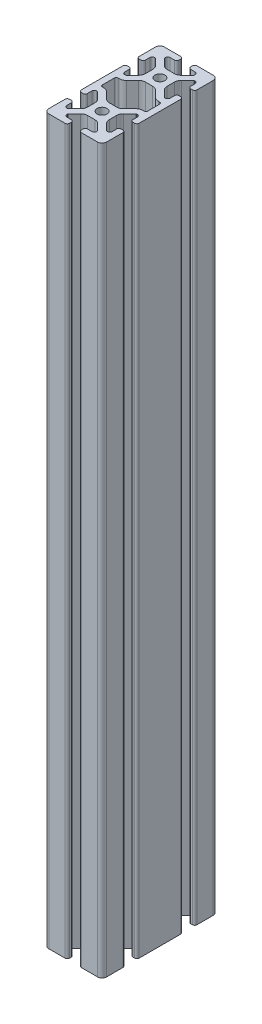
SolidWorks part; units mm, degrees
ref_plane "Front Plane" through (0, 0, 0) normal (0, 0, 1) x (1, 0, 0)
ref_plane "Top Plane" through (0, 0, 0) normal (0, 1, 0) x (1, 0, 0)
ref_plane "Right Plane" through (0, 0, 0) normal (1, 0, 0) x (0, 0, -1)
sketch3d "3DSketch1"
  line L0 (0, 0, 0) -> (0, 500, 0)
  dimension "D1" = 500
other "30 30-3060 PROFILE(1)"
ref_plane "Plane3" through (0, 0, 0) normal (0, 1, 0) x (1, 0, 0)
sketch "Sketch1" plane through (0, 0, 0) normal (0, 1, 0) x (1, 0, 0)
  line L0 (15.68, 24.125) -> (15.68, 15.875)
  line L1 (14.41, 14.605) -> (13.6545, 14.605)
  line L2 (10.0624, 13.1171) -> (5.8651, 8.9198)
  line L3 (2.5064, 7.5286) -> (-2.5064, 7.5286)
  line L4 (-5.8651, 8.9198) -> (-10.0624, 13.1171)
  line L5 (-13.6545, 14.605) -> (-14.41, 14.605)
  line L6 (-15.68, 15.875) -> (-15.68, 24.125)
  line L7 (-14.41, 25.395) -> (-13.6545, 25.395)
  line L8 (-10.0624, 26.8829) -> (-5.8651, 31.0802)
  line L9 (-2.5064, 32.4714) -> (2.5064, 32.4714)
  line L10 (5.8651, 31.0802) -> (10.0624, 26.8829)
  line L11 (13.6545, 25.395) -> (14.41, 25.395)
  line L12 (20, 5.63) -> (20, 34.37)
  line L13 (18.43, 35.94) -> (17.252, 35.94)
  line L14 (15.682, 34.37) -> (15.682, 31.285)
  line L15 (14.112, 29.715) -> (13.6545, 29.715)
  line L16 (13.1171, 29.9376) -> (8.9198, 34.1349)
  line L17 (7.5286, 37.4936) -> (7.5286, 42.5064)
  line L18 (8.9198, 45.8651) -> (13.1171, 50.0624)
  line L19 (13.6545, 50.285) -> (14.112, 50.285)
  line L20 (15.682, 48.715) -> (15.682, 45.63)
  line L21 (17.252, 44.06) -> (18.43, 44.06)
  line L22 (20, 45.63) -> (20, 56.83)
  line L23 (16.83, 60) -> (5.63, 60)
  line L24 (4.06, 58.43) -> (4.06, 57.252)
  line L25 (5.63, 55.682) -> (8.715, 55.682)
  line L26 (10.285, 54.112) -> (10.285, 53.6545)
  line L27 (10.0624, 53.1171) -> (5.8651, 48.9198)
  line L28 (2.5064, 47.5286) -> (-2.5064, 47.5286)
  line L29 (-5.8651, 48.9198) -> (-10.0624, 53.1171)
  line L30 (-10.285, 53.6545) -> (-10.285, 54.112)
  line L31 (-8.715, 55.682) -> (-5.63, 55.682)
  line L32 (-4.06, 57.252) -> (-4.06, 58.43)
  line L33 (-5.63, 60) -> (-16.83, 60)
  line L34 (-20, 56.83) -> (-20, 45.63)
  line L35 (-18.43, 44.06) -> (-17.252, 44.06)
  line L36 (-15.682, 45.63) -> (-15.682, 48.715)
  line L37 (-14.112, 50.285) -> (-13.6545, 50.285)
  line L38 (-13.1171, 50.0624) -> (-8.9198, 45.8651)
  line L39 (-7.5286, 42.5064) -> (-7.5286, 37.4936)
  line L40 (-8.9198, 34.1349) -> (-13.1171, 29.9376)
  line L41 (-13.6545, 29.715) -> (-14.112, 29.715)
  line L42 (-15.682, 31.285) -> (-15.682, 34.37)
  line L43 (-17.252, 35.94) -> (-18.43, 35.94)
  line L44 (-20, 34.37) -> (-20, 5.63)
  line L45 (-18.43, 4.06) -> (-17.252, 4.06)
  line L46 (-15.682, 5.63) -> (-15.682, 8.715)
  line L47 (-14.112, 10.285) -> (-13.6545, 10.285)
  line L48 (-13.1171, 10.0624) -> (-8.9198, 5.8651)
  line L49 (-7.5286, 2.5064) -> (-7.5286, -2.5064)
  line L50 (-8.9198, -5.8651) -> (-13.1171, -10.0624)
  line L51 (-13.6545, -10.285) -> (-14.112, -10.285)
  line L52 (-15.682, -8.715) -> (-15.682, -5.63)
  line L53 (-17.252, -4.06) -> (-18.43, -4.06)
  line L54 (-20, -5.63) -> (-20, -16.83)
  line L55 (-16.83, -20) -> (-5.63, -20)
  line L56 (-4.06, -18.43) -> (-4.06, -17.252)
  line L57 (-5.63, -15.682) -> (-8.715, -15.682)
  line L58 (-10.285, -14.112) -> (-10.285, -13.6545)
  line L59 (-10.0624, -13.1171) -> (-5.8651, -8.9198)
  line L60 (-2.5064, -7.5286) -> (2.5064, -7.5286)
  line L61 (5.8651, -8.9198) -> (10.0624, -13.1171)
  line L62 (10.285, -13.6545) -> (10.285, -14.112)
  line L63 (8.715, -15.682) -> (5.63, -15.682)
  line L64 (4.06, -17.252) -> (4.06, -18.43)
  line L65 (5.63, -20) -> (16.83, -20)
  line L66 (20, -16.83) -> (20, -5.63)
  line L67 (18.43, -4.06) -> (17.252, -4.06)
  line L68 (15.682, -5.63) -> (15.682, -8.715)
  line L69 (14.112, -10.285) -> (13.6545, -10.285)
  line L70 (13.1171, -10.0624) -> (8.9198, -5.8651)
  line L71 (7.5286, -2.5064) -> (7.5286, 2.5064)
  line L72 (8.9198, 5.8651) -> (13.1171, 10.0624)
  line L73 (13.6545, 10.285) -> (14.112, 10.285)
  line L74 (15.682, 8.715) -> (15.682, 5.63)
  line L75 (17.252, 4.06) -> (18.43, 4.06)
  circle A0 centre (0, 0) radius 3.4
  arc A1 (15.68, 24.125) -> (14.41, 25.395) centre (14.41, 24.125) ccw
  arc A2 (14.41, 14.605) -> (15.68, 15.875) centre (14.41, 15.875) ccw
  arc A3 (13.6545, 14.605) -> (10.0624, 13.1171) centre (13.6545, 9.525) ccw
  arc A4 (2.5064, 7.5286) -> (5.8651, 8.9198) centre (2.5064, 12.2786) ccw
  arc A5 (-5.8651, 8.9198) -> (-2.5064, 7.5286) centre (-2.5064, 12.2786) ccw
  arc A6 (-10.0624, 13.1171) -> (-13.6545, 14.605) centre (-13.6545, 9.525) ccw
  arc A7 (-15.68, 15.875) -> (-14.41, 14.605) centre (-14.41, 15.875) ccw
  arc A8 (-14.41, 25.395) -> (-15.68, 24.125) centre (-14.41, 24.125) ccw
  arc A9 (-13.6545, 25.395) -> (-10.0624, 26.8829) centre (-13.6545, 30.475) ccw
  arc A10 (-2.5064, 32.4714) -> (-5.8651, 31.0802) centre (-2.5064, 27.7214) ccw
  arc A11 (5.8651, 31.0802) -> (2.5064, 32.4714) centre (2.5064, 27.7214) ccw
  arc A12 (10.0624, 26.8829) -> (13.6545, 25.395) centre (13.6545, 30.475) ccw
  circle A13 centre (0, 40) radius 3.4
  arc A14 (18.43, 4.06) -> (20, 5.63) centre (18.43, 5.63) ccw
  arc A15 (20, 34.37) -> (18.43, 35.94) centre (18.43, 34.37) ccw
  arc A16 (17.252, 35.94) -> (15.682, 34.37) centre (17.252, 34.37) ccw
  arc A17 (14.112, 29.715) -> (15.682, 31.285) centre (14.112, 31.285) ccw
  arc A18 (13.1171, 29.9376) -> (13.6545, 29.715) centre (13.6545, 30.475) ccw
  arc A19 (7.5286, 37.4936) -> (8.9198, 34.1349) centre (12.2786, 37.4936) ccw
  arc A20 (8.9198, 45.8651) -> (7.5286, 42.5064) centre (12.2786, 42.5064) ccw
  arc A21 (13.6545, 50.285) -> (13.1171, 50.0624) centre (13.6545, 49.525) ccw
  arc A22 (15.682, 48.715) -> (14.112, 50.285) centre (14.112, 48.715) ccw
  arc A23 (15.682, 45.63) -> (17.252, 44.06) centre (17.252, 45.63) ccw
  arc A24 (18.43, 44.06) -> (20, 45.63) centre (18.43, 45.63) ccw
  arc A25 (20, 56.83) -> (16.83, 60) centre (16.83, 56.83) ccw
  arc A26 (5.63, 60) -> (4.06, 58.43) centre (5.63, 58.43) ccw
  arc A27 (4.06, 57.252) -> (5.63, 55.682) centre (5.63, 57.252) ccw
  arc A28 (10.285, 54.112) -> (8.715, 55.682) centre (8.715, 54.112) ccw
  arc A29 (10.0624, 53.1171) -> (10.285, 53.6545) centre (9.525, 53.6545) ccw
  arc A30 (2.5064, 47.5286) -> (5.8651, 48.9198) centre (2.5064, 52.2786) ccw
  arc A31 (-5.8651, 48.9198) -> (-2.5064, 47.5286) centre (-2.5064, 52.2786) ccw
  arc A32 (-10.285, 53.6545) -> (-10.0624, 53.1171) centre (-9.525, 53.6545) ccw
  arc A33 (-8.715, 55.682) -> (-10.285, 54.112) centre (-8.715, 54.112) ccw
  arc A34 (-5.63, 55.682) -> (-4.06, 57.252) centre (-5.63, 57.252) ccw
  arc A35 (-4.06, 58.43) -> (-5.63, 60) centre (-5.63, 58.43) ccw
  arc A36 (-16.83, 60) -> (-20, 56.83) centre (-16.83, 56.83) ccw
  arc A37 (-20, 45.63) -> (-18.43, 44.06) centre (-18.43, 45.63) ccw
  arc A38 (-17.252, 44.06) -> (-15.682, 45.63) centre (-17.252, 45.63) ccw
  arc A39 (-14.112, 50.285) -> (-15.682, 48.715) centre (-14.112, 48.715) ccw
  arc A40 (-13.1171, 50.0624) -> (-13.6545, 50.285) centre (-13.6545, 49.525) ccw
  arc A41 (-7.5286, 42.5064) -> (-8.9198, 45.8651) centre (-12.2786, 42.5064) ccw
  arc A42 (-8.9198, 34.1349) -> (-7.5286, 37.4936) centre (-12.2786, 37.4936) ccw
  arc A43 (-13.6545, 29.715) -> (-13.1171, 29.9376) centre (-13.6545, 30.475) ccw
  arc A44 (-15.682, 31.285) -> (-14.112, 29.715) centre (-14.112, 31.285) ccw
  arc A45 (-15.682, 34.37) -> (-17.252, 35.94) centre (-17.252, 34.37) ccw
  arc A46 (-18.43, 35.94) -> (-20, 34.37) centre (-18.43, 34.37) ccw
  arc A47 (-20, 5.63) -> (-18.43, 4.06) centre (-18.43, 5.63) ccw
  arc A48 (-17.252, 4.06) -> (-15.682, 5.63) centre (-17.252, 5.63) ccw
  arc A49 (-14.112, 10.285) -> (-15.682, 8.715) centre (-14.112, 8.715) ccw
  arc A50 (-13.1171, 10.0624) -> (-13.6545, 10.285) centre (-13.6545, 9.525) ccw
  arc A51 (-7.5286, 2.5064) -> (-8.9198, 5.8651) centre (-12.2786, 2.5064) ccw
  arc A52 (-8.9198, -5.8651) -> (-7.5286, -2.5064) centre (-12.2786, -2.5064) ccw
  arc A53 (-13.6545, -10.285) -> (-13.1171, -10.0624) centre (-13.6545, -9.525) ccw
  arc A54 (-15.682, -8.715) -> (-14.112, -10.285) centre (-14.112, -8.715) ccw
  arc A55 (-15.682, -5.63) -> (-17.252, -4.06) centre (-17.252, -5.63) ccw
  arc A56 (-18.43, -4.06) -> (-20, -5.63) centre (-18.43, -5.63) ccw
  arc A57 (-20, -16.83) -> (-16.83, -20) centre (-16.83, -16.83) ccw
  arc A58 (-5.63, -20) -> (-4.06, -18.43) centre (-5.63, -18.43) ccw
  arc A59 (-4.06, -17.252) -> (-5.63, -15.682) centre (-5.63, -17.252) ccw
  arc A60 (-10.285, -14.112) -> (-8.715, -15.682) centre (-8.715, -14.112) ccw
  arc A61 (-10.0624, -13.1171) -> (-10.285, -13.6545) centre (-9.525, -13.6545) ccw
  arc A62 (-2.5064, -7.5286) -> (-5.8651, -8.9198) centre (-2.5064, -12.2786) ccw
  arc A63 (5.8651, -8.9198) -> (2.5064, -7.5286) centre (2.5064, -12.2786) ccw
  arc A64 (10.285, -13.6545) -> (10.0624, -13.1171) centre (9.525, -13.6545) ccw
  arc A65 (8.715, -15.682) -> (10.285, -14.112) centre (8.715, -14.112) ccw
  arc A66 (5.63, -15.682) -> (4.06, -17.252) centre (5.63, -17.252) ccw
  arc A67 (4.06, -18.43) -> (5.63, -20) centre (5.63, -18.43) ccw
  arc A68 (16.83, -20) -> (20, -16.83) centre (16.83, -16.83) ccw
  arc A69 (20, -5.63) -> (18.43, -4.06) centre (18.43, -5.63) ccw
  arc A70 (17.252, -4.06) -> (15.682, -5.63) centre (17.252, -5.63) ccw
  arc A71 (14.112, -10.285) -> (15.682, -8.715) centre (14.112, -8.715) ccw
  arc A72 (13.1171, -10.0624) -> (13.6545, -10.285) centre (13.6545, -9.525) ccw
  arc A73 (7.5286, -2.5064) -> (8.9198, -5.8651) centre (12.2786, -2.5064) ccw
  arc A74 (8.9198, 5.8651) -> (7.5286, 2.5064) centre (12.2786, 2.5064) ccw
  arc A75 (13.6545, 10.285) -> (13.1171, 10.0624) centre (13.6545, 9.525) ccw
  arc A76 (15.682, 8.715) -> (14.112, 10.285) centre (14.112, 8.715) ccw
  arc A77 (15.682, 5.63) -> (17.252, 4.06) centre (17.252, 5.63) ccw
  point P0 (-20, 60)
  point P1 (0, 60)
  point P2 (20, 60)
  point P231 (20, 40)
  point P232 (-20, 40)
  point P233 (-20, 20)
  point P234 (0, 20)
  point P235 (20, 20)
  point P236 (20, 0)
  point P237 (20, -20)
  point P238 (0, -20)
  point P239 (-20, -20)
  point P240 (-20, 0)
  point P241 (0, 40)
  point P242 (0, 0)
